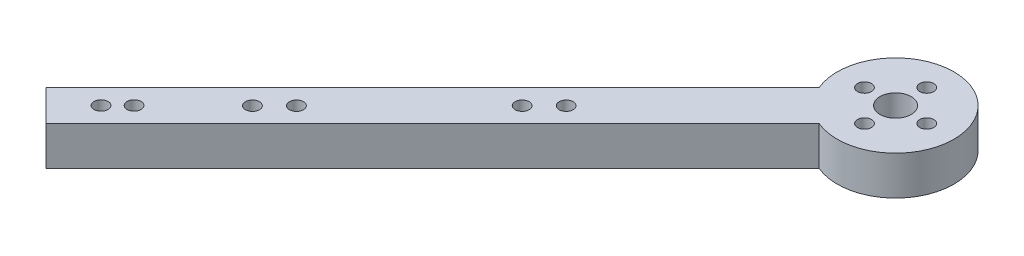
SolidWorks part; units mm, degrees
ref_plane "Front Plane" through (0, 0, 0) normal (0, 0, 1) x (1, 0, 0)
ref_plane "Top Plane" through (0, 0, 0) normal (0, 1, 0) x (1, 0, 0)
ref_plane "Right Plane" through (0, 0, 0) normal (1, 0, 0) x (0, 0, -1)
sketch "Sketch1" plane through (0, 0, 0) normal (0, 1, 0) x (1, 0, 0)
  circle A0 centre (0, 0) radius 9.525
  circle A1 centre (0, 0) radius 2.54
  circle A2 centre (-5.08, 0) radius 1.143
  circle A3 centre (0, 5.08) radius 1.143
  circle A4 centre (5.08, 0) radius 1.143
  circle A5 centre (0, -5.08) radius 1.143
  point P6 (0, 0)
  point P7 (0, 0)
  point P8 (0, 0)
  dimension "D1" = 5.08
  dimension "D2" = 2.286
  dimension "D5" = 19.05
  dimension "D3" = 5.08
  dimension "D4" = 4
extrude "Boss-Extrude1" add sketch "Sketch1" along normal blind 6.35
sketch "Sketch3" plane through (0, 0, 0) normal (0, 1, 0) x (1, 0, 0)
  line L12 (11.43, -133.35) -> (11.43, -146.05)
  line L13 (11.43, -146.05) -> (17.78, -152.4)
  line L14 (17.78, -152.4) -> (17.78, -127)
  line L15 (17.78, -127) -> (11.43, -133.35)
  line L16 (0, 5.08) -> (5.08, 0)
  line L17 (5.08, 0) -> (-66.762, -71.842)
  line L18 (0, 5.08) -> (-71.842, -66.762)
  line L19 (-71.842, -66.762) -> (-66.762, -71.842)
  arc A0 (-8.7779, -3.6979) -> (-3.6979, -8.7779) centre (0, 0) ccw
  circle A2 centre (0, 0) radius 9.525 construction
  point P2 (11.43, -139.7)
  point P5 (17.78, -139.7)
  dimension "D6" = 101.6
  dimension "D7" = 101.6
  dimension "D1" = 12.7
  dimension "D2" = 25.4
  dimension "D3" = 6.35
  dimension "D4" = 17.78
  dimension "D5" = 152.4
extrude "Boss-Extrude2" add sketch "Sketch3" along normal blind 6.35 contours L18 L19 L17 L16
sketch "Sketch4" plane through (0, 6.35, 0) normal (0, 1, 0) x (1, 0, 0)
  line L0 (-71.842, -66.762) -> (-66.762, -71.842) construction
  line L1 (-3.6979, -8.7779) -> (-66.762, -71.842) construction
  line L2 (-3.6979, -8.7779) -> (-66.762, -71.842) construction
  circle A0 centre (-64.821, -64.8028) radius 1.143
  circle A1 centre (-62.127, -62.1087) radius 1.143
  circle A2 centre (-52.4386, -52.4897) radius 1.143
  circle A3 centre (-48.8465, -48.8976) radius 1.143
  circle A4 centre (-30.437, -30.488) radius 1.143
  circle A5 centre (-26.8449, -26.8959) radius 1.143
  dimension "D1" = 2.286
  dimension "D2" = 2.286
  dimension "D7" = 2.286
  dimension "D8" = 2.286
  dimension "D14" = 2.286
  dimension "D15" = 2.286
  dimension "D3" = 6.35
  dimension "D4" = 3.81
  dimension "D5" = 3.605
  dimension "D6" = 3.605
  dimension "D9" = 5.08
  dimension "D10" = 3.556
  dimension "D11" = 3.556
  dimension "D12" = 13.6525
  dimension "D13" = 26.035
  dimension "D16" = 5.08
  dimension "D17" = 3.556
  dimension "D18" = 3.556
extrude "Cut-Extrude1" cut sketch "Sketch4" against normal blind 6.35
